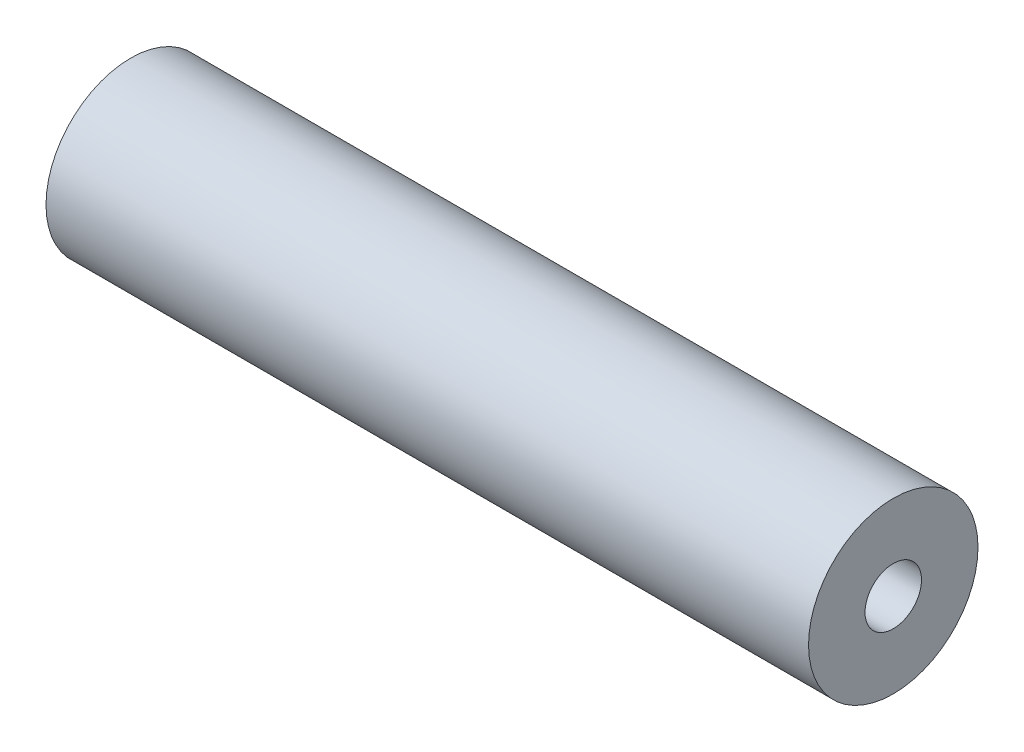
SolidWorks part; units mm, degrees
material "ABS"
ref_plane "Спереди" through (0, 0, 0) normal (0, 0, 1) x (1, 0, 0)
ref_plane "Сверху" through (0, 0, 0) normal (0, 1, 0) x (1, 0, 0)
ref_plane "Справа" through (0, 0, 0) normal (1, 0, 0) x (0, 0, -1)
sketch "Эскиз1" plane through (0, 0, 0) normal (1, 0, 0) x (0, 0, -1)
  circle A0 centre (0, 0) radius 6
extrude "Бобышка-Вытянуть1" add sketch "Эскиз1" along normal blind 54.0001
sketch "Эскиз2" plane through (0, 0, 0) normal (-1, 0, 0) x (0, 0, 1)
  circle A0 centre (0, 0) radius 2
extrude "Вырез-Вытянуть1" cut sketch "Эскиз2" against normal through all
